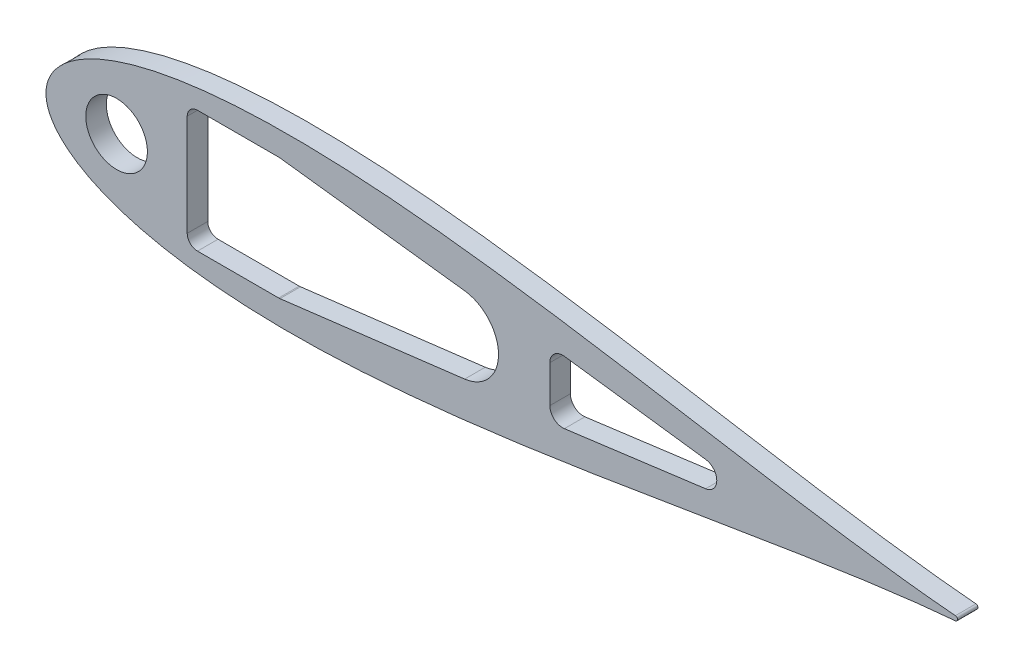
SolidWorks part; units mm, degrees
ref_plane "Front Plane" through (0, 0, 0) normal (0, 0, 1) x (1, 0, 0)
ref_plane "Top Plane" through (0, 0, 0) normal (0, 1, 0) x (1, 0, 0)
ref_plane "Right Plane" through (0, 0, 0) normal (1, 0, 0) x (0, 0, -1)
curve "Curve4"
  spline degree 3 poles (100, 0, 0) (99.8498, 0.0023, 0) (99.4759, 0.008, 0) (99.1023, 0.0238, 0) (98.8789, 0.0332, 0) knots 0 0 0 0 0.401829 1 1 1 1
curve "Curve5"
  spline degree 3 poles (99.3714, -0.0082, 0) (100.2526, 0, 0) (99.3714, 0.0082, 0) (98.8504, 0.035, 0) (97.904, 0.0811, 0) (96.8285, 0.1543, 0) (95.5159, 0.2583, 0) (94.013, 0.3972, 0) (92.313, 0.574, 0) (90.4281, 0.791, 0) (88.3655, 1.0495, 0) (86.1348, 1.3497, 0) (83.7456, 1.691, 0) (81.2082, 2.0715, 0) (78.5335, 2.4886, 0) (75.7326, 2.9386, 0) (72.8172, 3.4168, 0) (69.799, 3.9177, 0) (66.6904, 4.435, 0) (63.5039, 4.9616, 0) (60.2521, 5.4899, 0) (56.948, 6.0119, 0) (53.6049, 6.519, 0) (50.2363, 7.0024, 0) (46.8558, 7.4534, 0) (43.4774, 7.8632, 0) (40.1152, 8.2232, 0) (36.7837, 8.5249, 0) (33.4975, 8.7606, 0) (30.2716, 8.923, 0) (27.1211, 9.0055, 0) (24.0614, 9.0025, 0) (21.108, 8.909, 0) (18.277, 8.7213, 0) (15.5843, 8.4369, 0) (13.0466, 8.0543, 0) (10.6806, 7.5735, 0) (8.5039, 6.996, 0) (6.5349, 6.3253, 0) (4.7933, 5.5673, 0) (3.3001, 4.7321, 0) (2.0777, 3.8366, 0) (1.1467, 2.91, 0) (0.5165, 2.0014, 0) (0.165, 1.1816, 0) (0.0231, 0.524, 0) (-0.0093, 0, 0) (0.0231, -0.524, 0) (0.165, -1.1816, 0) (0.5165, -2.0014, 0) (1.1467, -2.91, 0) (2.0777, -3.8366, 0) (3.3001, -4.7321, 0) (4.7933, -5.5673, 0) (6.5349, -6.3253, 0) (8.5039, -6.996, 0) (10.6806, -7.5735, 0) (13.0466, -8.0543, 0) (15.5843, -8.4369, 0) (18.277, -8.7213, 0) (21.108, -8.909, 0) (24.0614, -9.0025, 0) (27.1211, -9.0055, 0) (30.2716, -8.923, 0) (33.4975, -8.7606, 0) (36.7837, -8.5249, 0) (40.1152, -8.2232, 0) (43.4774, -7.8632, 0) (46.8558, -7.4534, 0) (50.2363, -7.0024, 0) (53.6049, -6.519, 0) (56.948, -6.0119, 0) (60.2521, -5.4899, 0) (63.5039, -4.9616, 0) (66.6904, -4.435, 0) (69.799, -3.9177, 0) (72.8172, -3.4168, 0) (75.7326, -2.9386, 0) (78.5335, -2.4886, 0) (81.2082, -2.0715, 0) (83.7456, -1.691, 0) (86.1348, -1.3497, 0) (88.3655, -1.0495, 0) (90.4281, -0.791, 0) (92.313, -0.574, 0) (94.013, -0.3972, 0) (95.5159, -0.2583, 0) (96.8285, -0.1543, 0) (97.904, -0.0811, 0) (98.8504, -0.035, 0) (99.3714, -0.0082, 0) (100.2526, 0, 0) (99.3714, 0.0082, 0) knots -0.009667 -0.005395 -0.002168 0 0.002168 0.005395 0.009667 0.014967 0.021271 0.028553 0.036781 0.04592 0.055932 0.066773 0.078397 0.090755 0.103793 0.117456 0.131686 0.146422 0.1616 0.177156 0.193024 0.209135 0.225421 0.241812 0.258238 0.274629 0.290914 0.307025 0.322893 0.338448 0.353626 0.368361 0.38259 0.396253 0.40929 0.421647 0.43327 0.444109 0.454119 0.463255 0.471479 0.478755 0.485052 0.490344 0.49461 0.497833 0.5 0.502167 0.50539 0.509656 0.514948 0.521245 0.528521 0.536745 0.545881 0.555891 0.56673 0.578353 0.59071 0.603747 0.61741 0.631639 0.646374 0.661552 0.677107 0.692975 0.709086 0.725371 0.741762 0.758188 0.774579 0.790865 0.806976 0.822844 0.8384 0.853578 0.868314 0.882544 0.896207 0.909245 0.921603 0.933227 0.944068 0.95408 0.963219 0.971447 0.978729 0.985033 0.990333 0.994605 0.997832 1 1.002168 1.005395 1.009667 periodic
sketch "Sketch2" plane through (0, 0, 0) normal (0, 0, 1) x (1, 0, 0)
  line L0 (642.3793, 0) -> (0, 0) construction
  circle A14 centre (642.3793, 0) radius 1.5875 construction
  arc A15 (642.5108, -1.582) -> (642.5108, 1.582) centre (642.3793, 0) ccw
  spline S2 degree 3 poles (666.3448, -0.0547) (672.2538, 0) (666.3448, 0.0547) (662.8509, 0.2344) (656.505, 0.5436) (649.293, 1.0348) (640.4916, 1.7319) (630.4138, 2.6634) (619.0141, 3.8493) (606.375, 5.3044) (592.5439, 7.0376) (577.5855, 9.0506) (561.5643, 11.3389) (544.5497, 13.8907) (526.6141, 16.6877) (507.8326, 19.7051) (488.2827, 22.9117) (468.0444, 26.2704) (447.1994, 29.739) (425.8316, 33.2703) (404.0263, 36.8132) (381.8707, 40.3133) (359.4533, 43.7135) (336.8645, 46.9554) (314.1962, 49.9798) (291.5418, 52.7277) (268.9963, 55.1412) (246.6566, 57.1646) (224.6209, 58.7452) (202.9892, 59.8341) (181.8631, 60.3875) (161.3458, 60.367) (141.542, 59.7399) (122.5581, 58.4818) (104.5023, 56.5743) (87.485, 54.0089) (71.6197, 50.7848) (57.0237, 46.9125) (43.8205, 42.415) (32.1416, 37.3322) (22.1291, 31.7315) (13.9324, 25.7264) (7.6896, 19.5132) (3.4631, 13.4204) (1.1063, 7.9234) (0.1546, 3.5138) (-0.0622, 0) (0.1546, -3.5138) (1.1063, -7.9234) (3.4631, -13.4204) (7.6896, -19.5132) (13.9324, -25.7264) (22.1291, -31.7315) (32.1416, -37.3322) (43.8205, -42.415) (57.0237, -46.9125) (71.6197, -50.7848) (87.485, -54.0089) (104.5023, -56.5743) (122.5581, -58.4818) (141.542, -59.7399) (161.3458, -60.367) (181.8631, -60.3875) (202.9892, -59.8341) (224.6209, -58.7452) (246.6566, -57.1646) (268.9963, -55.1412) (291.5418, -52.7277) (314.1962, -49.9798) (336.8645, -46.9554) (359.4533, -43.7135) (381.8707, -40.3133) (404.0263, -36.8132) (425.8316, -33.2703) (447.1994, -29.739) (468.0444, -26.2704) (488.2827, -22.9117) (507.8326, -19.7051) (526.6141, -16.6877) (544.5497, -13.8907) (561.5643, -11.3389) (577.5855, -9.0506) (592.5439, -7.0376) (606.375, -5.3044) (619.0141, -3.8493) (630.4138, -2.6634) (640.4916, -1.7319) (649.293, -1.0348) (656.505, -0.5436) (662.8509, -0.2344) (666.3448, -0.0547) (672.2538, 0) (666.3448, 0.0547) knots -0.009667 -0.005395 -0.002168 0 0.002168 0.005395 0.009667 0.014967 0.021271 0.028553 0.036781 0.04592 0.055932 0.066773 0.078397 0.090755 0.103793 0.117456 0.131686 0.146422 0.1616 0.177156 0.193024 0.209135 0.225421 0.241812 0.258238 0.274629 0.290914 0.307025 0.322893 0.338448 0.353626 0.368361 0.38259 0.396253 0.40929 0.421647 0.43327 0.444109 0.454119 0.463255 0.471479 0.478755 0.485052 0.490344 0.49461 0.497833 0.5 0.502167 0.50539 0.509656 0.514948 0.521245 0.528521 0.536745 0.545881 0.555891 0.56673 0.578353 0.59071 0.603747 0.61741 0.631639 0.646374 0.661552 0.677107 0.692975 0.709086 0.725371 0.741762 0.758188 0.774579 0.790865 0.806976 0.822844 0.8384 0.853578 0.868314 0.882544 0.896207 0.909245 0.921603 0.933227 0.944068 0.95408 0.963219 0.971447 0.978729 0.985033 0.990333 0.994605 0.997832 1 1.002168 1.005395 1.009667 only from (670.56, 0) to (670.56, 0)
  point P8 (1.2169, -4.6585)
  point P10 (1.2169, 4.6585)
  dimension "D10" = 3.175
extrude "Boss-Extrude1" add sketch "Sketch2" along normal blind 5.4737
extrude "Cut-Extrude4" cut sketch "Sketch7" against normal through all
sketch "Sketch7" plane through (327.9592, -13.7514, 6.35) normal (0, 0, 1) x (1, 0, 0)
  line L1 (-154.9852, -16.7286) -> (-66.0852, -16.7286)
  line L2 (-154.9852, -16.7286) -> (-154.9852, 44.2314)
  line L3 (-154.9852, 44.2314) -> (-66.0852, 44.2314)
  line L4 (-66.0852, -16.7286) -> (-66.0852, 44.2314)
  line L5 (-154.9852, -16.7286) -> (-66.0852, 44.2314) construction
  line L6 (-154.9852, 44.2314) -> (-66.0852, -16.7286) construction
  point P0 (-110.5352, 13.7514)
extrude "Cut-Extrude5" cut sketch "Sketch8" against normal through all
sketch "Sketch8" plane through (327.9592, -13.7514, 6.35) normal (0, 0, 1) x (1, 0, 0)
  circle A0 centre (314.9285, 13.7514) radius 1.2446
scale "Scale1" bodies to scale 101 scale about origin uniform scaling yes scale factor 0.35
sketch "Sketch11" plane through (0, 0, 0) normal (0, 0, -1) x (-1, 0, 0)
  arc A1 (-224.8788, 0.5537) -> (-224.8788, -0.5537) centre (-224.8328, 0) ccw
  arc A2 (-224.8788, 0.5537) -> (-224.8788, -0.5537) centre (-224.8328, 0) ccw
  spline S1 degree 3 poles (1767.0875, -177.9163) (-335.1087, -6.3319) (-273.2817, 3.9329) (-220.6448, -0.9322) (-216.6549, -1.3472) (-212.2312, -1.8566) (-207.3904, -2.4632) (-202.1549, -3.1677) (-196.5475, -3.9686) (-190.5924, -4.8617) (-184.315, -5.8407) (-177.7414, -6.8968) (-170.8989, -8.0191) (-163.8155, -9.1947) (-156.5198, -10.4087) (-149.0411, -11.6446) (-141.4092, -12.8846) (-133.6547, -14.1096) (-125.8087, -15.2997) (-117.9026, -16.4344) (-109.9687, -17.4929) (-102.0396, -18.4547) (-94.1487, -19.2994) (-86.3298, -20.0076) (-78.6173, -20.5608) (-71.0462, -20.9419) (-63.6521, -21.1356) (-56.471, -21.1284) (-49.5397, -20.909) (-42.8953, -20.4686) (-36.5758, -19.801) (-30.6198, -18.9031) (-25.0669, -17.7747) (-19.9583, -16.4194) (-15.3372, -14.8453) (-11.2496, -13.0663) (-7.7452, -11.106) (-4.8763, -9.0042) (-2.6914, -6.8296) (-1.2121, -4.6971) (-0.3872, -2.7732) (-0.0541, -1.2298) (0.0218, 0) (-0.0541, 1.2298) (-0.3872, 2.7732) (-1.2121, 4.6971) (-2.6914, 6.8296) (-4.8763, 9.0042) (-7.7452, 11.106) (-11.2496, 13.0663) (-15.3372, 14.8453) (-19.9583, 16.4194) (-25.0669, 17.7747) (-30.6198, 18.9031) (-36.5758, 19.801) (-42.8953, 20.4686) (-49.5397, 20.909) (-56.471, 21.1284) (-63.6521, 21.1356) (-71.0462, 20.9419) (-78.6173, 20.5608) (-86.3298, 20.0076) (-94.1487, 19.2994) (-102.0396, 18.4547) (-109.9687, 17.4929) (-117.9026, 16.4344) (-125.8087, 15.2997) (-133.6547, 14.1096) (-141.4092, 12.8846) (-149.0411, 11.6446) (-156.5198, 10.4087) (-163.8155, 9.1947) (-170.8989, 8.0191) (-177.7414, 6.8968) (-184.315, 5.8407) (-190.5924, 4.8617) (-196.5475, 3.9686) (-202.1549, 3.1677) (-207.3904, 2.4632) (-212.2312, 1.8566) (-216.6549, 1.3472) (-220.6448, 0.9322) (-273.2815, -3.9329) (-335.1083, 6.3319) (1767.0695, 177.9148) knots -0.28875 -0.28875 -0.28875 -0.28875 0.021271 0.028553 0.036781 0.04592 0.055932 0.066773 0.078397 0.090755 0.103793 0.117456 0.131686 0.146422 0.1616 0.177156 0.193024 0.209135 0.225421 0.241812 0.258238 0.274629 0.290914 0.307025 0.322893 0.338448 0.353626 0.368361 0.38259 0.396253 0.40929 0.421647 0.43327 0.444109 0.454119 0.463255 0.471479 0.478755 0.485052 0.490344 0.49461 0.497833 0.5 0.502167 0.50539 0.509656 0.514948 0.521245 0.528521 0.536745 0.545881 0.555891 0.56673 0.578353 0.59071 0.603747 0.61741 0.631639 0.646374 0.661552 0.677107 0.692975 0.709086 0.725371 0.741762 0.758188 0.774579 0.790865 0.806976 0.822844 0.8384 0.853578 0.868314 0.882544 0.896207 0.909245 0.921603 0.933227 0.944068 0.95408 0.963219 0.971447 0.978729 1.288749 1.288749 1.288749 1.288749 only from (-224.8788, -0.5537) to (-224.8788, 0.5537)
  spline S2 degree 3 poles (-224.8788, -0.5537) (-224.6977, -0.5688) (-223.3328, -0.6837) (-220.6448, -0.9322) (-216.6549, -1.3472) (-212.2312, -1.8566) (-207.3904, -2.4632) (-202.1549, -3.1677) (-196.5475, -3.9686) (-190.5924, -4.8617) (-184.315, -5.8407) (-177.7414, -6.8968) (-170.8989, -8.0191) (-163.8155, -9.1947) (-156.5198, -10.4087) (-149.0411, -11.6446) (-141.4092, -12.8846) (-133.6547, -14.1096) (-125.8087, -15.2997) (-117.9026, -16.4344) (-109.9687, -17.4929) (-102.0396, -18.4547) (-94.1487, -19.2994) (-86.3298, -20.0076) (-78.6173, -20.5608) (-71.0462, -20.9419) (-63.6521, -21.1356) (-56.471, -21.1284) (-49.5397, -20.909) (-42.8953, -20.4686) (-36.5758, -19.801) (-30.6198, -18.9031) (-25.0669, -17.7747) (-19.9583, -16.4194) (-15.3372, -14.8453) (-11.2496, -13.0663) (-7.7452, -11.106) (-4.8763, -9.0042) (-2.6914, -6.8296) (-1.2121, -4.6971) (-0.3872, -2.7732) (-0.0541, -1.2298) (0.0218, 0) (-0.0541, 1.2298) (-0.3872, 2.7732) (-1.2121, 4.6971) (-2.6914, 6.8296) (-4.8763, 9.0042) (-7.7452, 11.106) (-11.2496, 13.0663) (-15.3372, 14.8453) (-19.9583, 16.4194) (-25.0669, 17.7747) (-30.6198, 18.9031) (-36.5758, 19.801) (-42.8953, 20.4686) (-49.5397, 20.909) (-56.471, 21.1284) (-63.6521, 21.1356) (-71.0462, 20.9419) (-78.6173, 20.5608) (-86.3298, 20.0076) (-94.1487, 19.2994) (-102.0396, 18.4547) (-109.9687, 17.4929) (-117.9026, 16.4344) (-125.8087, 15.2997) (-133.6547, 14.1096) (-141.4092, 12.8846) (-149.0411, 11.6446) (-156.5198, 10.4087) (-163.8155, 9.1947) (-170.8989, 8.0191) (-177.7414, 6.8968) (-184.315, 5.8407) (-190.5924, 4.8617) (-196.5475, 3.9686) (-202.1549, 3.1677) (-207.3904, 2.4632) (-212.2312, 1.8566) (-216.6549, 1.3472) (-220.6448, 0.9322) (-223.3328, 0.6837) (-224.6977, 0.5688) (-224.8788, 0.5537) knots 0.020157 0.020157 0.020157 0.020157 0.021271 0.028553 0.036781 0.04592 0.055932 0.066773 0.078397 0.090755 0.103793 0.117456 0.131686 0.146422 0.1616 0.177156 0.193024 0.209135 0.225421 0.241812 0.258238 0.274629 0.290914 0.307025 0.322893 0.338448 0.353626 0.368361 0.38259 0.396253 0.40929 0.421647 0.43327 0.444109 0.454119 0.463255 0.471479 0.478755 0.485052 0.490344 0.49461 0.497833 0.5 0.502167 0.50539 0.509656 0.514948 0.521245 0.528521 0.536745 0.545881 0.555891 0.56673 0.578353 0.59071 0.603747 0.61741 0.631639 0.646374 0.661552 0.677107 0.692975 0.709086 0.725371 0.741762 0.758188 0.774579 0.790865 0.806976 0.822844 0.8384 0.853578 0.868314 0.882544 0.896207 0.909245 0.921603 0.933227 0.944068 0.95408 0.963219 0.971447 0.978729 0.979843 0.979843 0.979843 0.979843
  dimension "D1" = 0
extrude "Boss-Extrude2" add sketch "Sketch11" against normal blind 5.08
sketch "Sketch10" plane through (0, 0, 0) normal (0, 0, 1) x (1, 0, 0)
  line L1 (34.925, -15.0812) -> (60.0922, -15.0812)
  line L2 (34.925, -15.0812) -> (34.925, 15.0812)
  line L3 (34.925, 15.0812) -> (60.0922, 15.0812)
  line L4 (60.0922, -15.0812) -> (60.0922, 15.0812)
  line L5 (34.925, -15.0812) -> (60.0922, 15.0812) construction
  line L6 (34.925, 15.0812) -> (60.0922, -15.0812) construction
  arc A2 (224.8788, -0.5537) -> (224.8788, 0.5537) centre (224.8328, 0) ccw
  arc A3 (224.8788, -0.5537) -> (224.8788, 0.5537) centre (224.8328, 0) ccw construction
  spline S1 degree 3 poles (-770.5569, 95.104) (312.0087, 2.9748) (263.5397, -3.0325) (220.6448, 0.9322) (216.6549, 1.3472) (212.2312, 1.8566) (207.3904, 2.4632) (202.1549, 3.1677) (196.5475, 3.9686) (190.5924, 4.8617) (184.315, 5.8407) (177.7414, 6.8968) (170.8989, 8.0191) (163.8155, 9.1947) (156.5198, 10.4087) (149.0411, 11.6446) (141.4092, 12.8846) (133.6547, 14.1096) (125.8087, 15.2997) (117.9026, 16.4344) (109.9687, 17.4929) (102.0396, 18.4547) (94.1487, 19.2994) (86.3298, 20.0076) (78.6173, 20.5608) (71.0462, 20.9419) (63.6521, 21.1356) (56.471, 21.1284) (49.5397, 20.909) (42.8953, 20.4686) (36.5758, 19.801) (30.6198, 18.9031) (25.0669, 17.7747) (19.9583, 16.4194) (15.3372, 14.8453) (11.2496, 13.0663) (7.7452, 11.106) (4.8763, 9.0042) (2.6914, 6.8296) (1.2121, 4.6971) (0.3872, 2.7732) (0.0541, 1.2298) (-0.0218, 0) (0.0541, -1.2298) (0.3872, -2.7732) (1.2121, -4.6971) (2.6914, -6.8296) (4.8763, -9.0042) (7.7452, -11.106) (11.2496, -13.0663) (15.3372, -14.8453) (19.9583, -16.4194) (25.0669, -17.7747) (30.6198, -18.9031) (36.5758, -19.801) (42.8953, -20.4686) (49.5397, -20.909) (56.471, -21.1284) (63.6521, -21.1356) (71.0462, -20.9419) (78.6173, -20.5608) (86.3298, -20.0076) (94.1487, -19.2994) (102.0396, -18.4547) (109.9687, -17.4929) (117.9026, -16.4344) (125.8087, -15.2997) (133.6547, -14.1096) (141.4092, -12.8846) (149.0411, -11.6446) (156.5198, -10.4087) (163.8155, -9.1947) (170.8989, -8.0191) (177.7414, -6.8968) (184.315, -5.8407) (190.5924, -4.8617) (196.5475, -3.9686) (202.1549, -3.1677) (207.3904, -2.4632) (212.2312, -1.8566) (216.6549, -1.3472) (220.6448, -0.9322) (263.5395, 3.0325) (312.0083, -2.9748) (-770.5417, -95.1027) knots -0.228501 -0.228501 -0.228501 -0.228501 0.021271 0.028553 0.036781 0.04592 0.055932 0.066773 0.078397 0.090755 0.103793 0.117456 0.131686 0.146422 0.1616 0.177156 0.193024 0.209135 0.225421 0.241812 0.258238 0.274629 0.290914 0.307025 0.322893 0.338448 0.353626 0.368361 0.38259 0.396253 0.40929 0.421647 0.43327 0.444109 0.454119 0.463255 0.471479 0.478755 0.485052 0.490344 0.49461 0.497833 0.5 0.502167 0.50539 0.509656 0.514948 0.521245 0.528521 0.536745 0.545881 0.555891 0.56673 0.578353 0.59071 0.603747 0.61741 0.631639 0.646374 0.661552 0.677107 0.692975 0.709086 0.725371 0.741762 0.758188 0.774579 0.790865 0.806976 0.822844 0.8384 0.853578 0.868314 0.882544 0.896207 0.909245 0.921603 0.933227 0.944068 0.95408 0.963219 0.971447 0.978729 1.2285 1.2285 1.2285 1.2285 only from (224.8788, 0.5537) to (224.8788, -0.5537)
  point P0 (47.5086, 0)
  dimension "D1" = 25.1672
  dimension "D2" = 34.925
  dimension "D5" = 30.1625
  dimension "D3" = 0
extrude "Cut-Extrude6" cut sketch "Sketch10" along normal through all
fillet "Fillet1" radius 2.54 4 edges at (60.0922, -15.0812, 2.54) (34.925, -15.0812, 2.54) (34.925, 15.0812, 2.54) (60.0922, 15.0812, 2.54)
hole_wizard "#8 Clearance Hole1" positions "Sketch12" profile "Sketch13" hole size "#8" standard "ANSI Inch"
sketch "Sketch12" plane through (0, 0, 5.08) normal (0, 0, 1) x (1, 0, 0)
  line L0 (76.2, 0) -> (0, 0) construction
  line L2 (31.75, 8.8646) -> (31.75, -8.8646) construction
  point P0 (12.7, 0)
  point P2 (76.2, 0)
  dimension "D1" = 19.05
  dimension "D2" = 44.45
sketch "Sketch13" plane through (12.7, 0, 5.08) normal (1, 0, 0) x (0, -1, 0)
  line L0 (0, 0) -> (0, 5.08)
  line L1 (0, 5.08) -> (2.2479, 5.08)
  line L2 (2.2479, 5.08) -> (2.2479, 0)
  line L5 (2.2479, 0) -> (0, 0)
  line L11 (0, -6.35) -> (0, 107.95) construction
  dimension "Thru Hole Dia." = 4.4958
  dimension "Thru Hole Depth" = 5.08
sketch "Sketch15" plane through (0, 0, 5.08) normal (0, 0, 1) x (1, 0, 0)
  line L0 (35.6689, 14.3373) -> (59.3482, -14.3373)
  line L1 (24.0679, 12.7) -> (74.8679, -12.7) construction
  line L2 (26.6079, 12.7) -> (72.3279, 12.7)
  line L3 (24.0679, 10.16) -> (24.0679, -10.16)
  line L4 (26.6079, -12.7) -> (72.3279, -12.7)
  line L5 (74.8679, 10.16) -> (74.8679, -10.16)
  circle A0 centre (47.5086, 0) radius 13.716
  arc A1 (37.465, 15.0812) -> (34.925, 12.5412) centre (37.465, 12.5412) ccw construction
  arc A2 (57.5522, -15.0812) -> (60.0922, -12.5412) centre (57.5522, -12.5412) ccw construction
  arc A3 (72.3279, 12.7) -> (74.8679, 10.16) centre (72.3279, 10.16) cw
  arc A4 (74.8679, -10.16) -> (72.3279, -12.7) centre (72.3279, -10.16) cw
  arc A5 (26.6079, -12.7) -> (24.0679, -10.16) centre (26.6079, -10.16) cw
  arc A6 (26.6079, 12.7) -> (24.0679, 10.16) centre (26.6079, 10.16) ccw
  point P10 (49.4679, 0)
  point P18 (74.8679, 12.7)
  dimension "D1" = 27.432
  dimension "D4" = 2.54
  dimension "D2" = 50.8
  dimension "D3" = 25.4
sketch "Sketch16" plane through (0, 0, 5.08) normal (0, 0, 1) x (1, 0, 0)
  line L0 (102.3726, 0) -> (100.5946, 0) construction
  line L1 (102.3726, -9.525) -> (100.5946, -9.525)
  line L2 (102.3726, 9.525) -> (100.5946, 9.525)
  arc A0 (102.3726, -9.525) -> (102.3726, 9.525) centre (102.3726, 0) ccw
  arc A1 (100.5946, 9.525) -> (100.5946, -9.525) centre (100.5946, 0) ccw
  point P3 (101.4836, 0)
  dimension "D1" = 9.525
  dimension "D2" = 1.778
  dimension "D3" = 53.975
extrude "Cut-Extrude8" cut sketch "Sketch16" against normal through all
sketch "Sketch18" plane through (0, 0, 5.08) normal (0, 0, 1) x (1, 0, 0)
  line L2 (57.8617, 15.0623) -> (103.5335, 9.454)
  line L4 (103.5335, -9.454) -> (57.8617, -15.0623)
  line L5 (60.0922, -12.5412) -> (60.0922, 12.5412) construction
  line L8 (60.0922, -12.5412) -> (60.0922, 12.5412)
  arc A0 (60.0922, 12.5412) -> (57.5522, 15.0812) centre (57.5522, 12.5412) ccw construction
  arc A3 (102.3726, -9.525) -> (102.3726, 9.525) centre (102.3726, 0) ccw construction
  arc A4 (57.5522, -15.0812) -> (60.0922, -12.5412) centre (57.5522, -12.5412) ccw construction
  arc A6 (103.5335, -9.454) -> (103.5335, 9.454) centre (102.3726, 0) ccw
  arc A8 (57.8617, -15.0623) -> (60.0922, -12.5412) centre (57.5522, -12.5412) ccw
  arc A9 (60.0922, 12.5412) -> (57.8617, 15.0623) centre (57.5522, 12.5412) ccw
extrude "Cut-Extrude9" cut sketch "Sketch18" against normal through all
sketch "Sketch19" plane through (0, 0, 5.08) normal (0, 0, 1) x (1, 0, 0)
  line L0 (34.925, 0) -> (0, 0) construction
  line L1 (34.925, 12.5412) -> (34.925, -12.5412) construction
  line L2 (163.112, 3.1478) -> (128.187, 7.7458)
  line L3 (124.5976, 4.598) -> (124.5976, -4.598)
  line L4 (128.187, -7.7458) -> (163.112, -3.1478)
  circle A0 centre (17.4625, 0) radius 7.62
  arc A1 (163.112, -3.1478) -> (163.112, 3.1478) centre (162.6976, 0) ccw
  arc A2 (103.5335, -9.454) -> (103.5335, 9.454) centre (102.3726, 0) ccw construction
  arc A3 (128.187, -7.7458) -> (124.5976, -4.598) centre (127.7726, -4.598) cw
  arc A4 (124.5976, 4.598) -> (128.187, 7.7458) centre (127.7726, 4.598) cw
  point P13 (111.8976, 0)
  point P17 (124.5976, 0)
  dimension "D1" = 15.24
  dimension "D2" = 6.35
  dimension "D4" = 3.175
  dimension "D3" = 50.8
  dimension "D5" = 15
  dimension "D6" = 12.7
extrude "Cut-Extrude10" cut sketch "Sketch19" against normal through all
equation "\"0.5n\"=0"
equation "\"D1@Sketch10\"=0.898/cos(25deg)"
